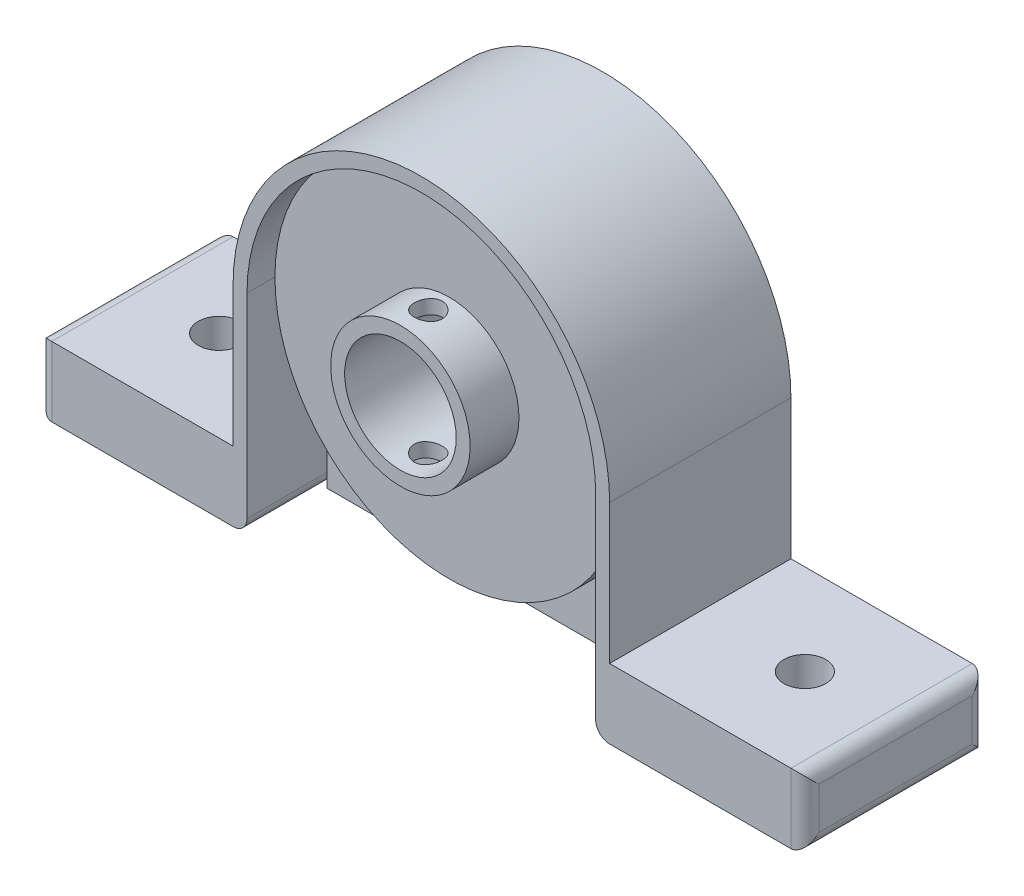
SolidWorks part; units mm, degrees
material "Cast Alloy Steel"
ref_plane "Front Plane" through (0, 0, 0) normal (0, 0, 1) x (1, 0, 0)
ref_plane "Top Plane" through (0, 0, 0) normal (0, 1, 0) x (1, 0, 0)
ref_plane "Right Plane" through (0, 0, 0) normal (1, 0, 0) x (0, 0, -1)
sketch "Sketch3" plane through (0, 0, 0) normal (0, 0, 1) x (1, 0, 0)
  line L0 (0, 0) -> (15, 0)
  line L1 (0, 0) -> (0, 5)
  line L2 (0, 5) -> (14, 5)
  line L3 (55, 0) -> (55, 5)
  line L4 (55, 5) -> (41, 5)
  line L5 (27.5, 0) -> (27.5, 15) construction
  line L6 (14, 5) -> (14, 15)
  line L7 (41, 5) -> (41, 15)
  line L8 (15, 15) -> (15, 0)
  line L9 (40, 15) -> (40, 0)
  line L10 (40, 0) -> (55, 0)
  arc A0 (15, 9.901) -> (40, 9.901) centre (27.5, 15) ccw
  circle A1 centre (27.5, 15) radius 12.5
  arc A2 (41, 15) -> (14, 15) centre (27.5, 15) ccw
  dimension "D6" = 27
  dimension "D3" = 25
  dimension "D1" = 55
  dimension "D2" = 5
  dimension "D5" = 15
extrude "Boss-Extrude1" add sketch "Sketch3" along normal blind 13
ref_plane "Plane1" through (0, 2, 0) normal (0, 1, 0) x (1, 0, 0)
sketch "Sketch6" plane through (0, 0, 13) normal (0, 0, 1) x (1, 0, 0)
  circle A0 centre (27.5, 15) radius 12.5
  circle A1 centre (27.5, 15) radius 5
  dimension "D1" = 10
extrude "Cut-Extrude2" cut sketch "Sketch6" against normal blind 2
ref_plane "Plane2" through (0, 0, 6.5) normal (0, 0, 1) x (1, 0, 0)
mirror "Mirror1" about plane through (0, 0, 6.5) normal (0, 0, 1) of "Cut-Extrude2"
sketch "Sketch7" plane through (0, 0, 13) normal (0, 0, 1) x (1, 0, 0)
  circle A0 centre (27.5, 15) radius 4.5
  dimension "D1" = 9
extrude "Cut-Extrude5" cut sketch "Sketch7" against normal blind 1.75
sketch "Sketch8" plane through (0, 0, 0) normal (0, 0, -1) x (-1, 0, 0)
  circle A0 centre (-27.5, 15) radius 4
  point P4 (-27.5, 15)
  dimension "D1" = 8
sketch "Sketch9" plane through (0, 0, 0) normal (0, 0, -1) x (-1, 0, 0)
  circle A0 centre (-27.5, 15) radius 5
extrude "Cut-Extrude6" cut sketch "Sketch9" against normal blind 1.75
sketch "Sketch10" plane through (0, 0, 11.25) normal (0, 0, 1) x (1, 0, 0)
  circle A0 centre (27.5, 15) radius 5
  dimension "D1" = 10
extrude "Boss-Extrude4" add sketch "Sketch10" along normal blind 3.25
sketch "Sketch11" plane through (0, 0, 14.5) normal (0, 0, 1) x (1, 0, 0)
  circle A0 centre (27.5, 15) radius 4
  dimension "D1" = 8
extrude "Cut-Extrude7" cut sketch "Sketch11" against normal through all
ref_plane "Plane3" through (27.5, 0, 0) normal (1, 0, 0) x (0, 0, -1)
fillet "Fillet1" radius 1 8 edges at (0, 2.5, 13) (0, 0, 6.5) (0, 2.5, 0) (0, 5, 6.5) (55, 2.5, 0) (55, 2.5, 13) (55, 0, 6.5) (55, 5, 6.5)
fillet "Fillet2" radius 1 2 edges at (40, 0, 6.5) (15, 0, 6.5)
ref_plane "Plane4" through (0, 14.25, 0) normal (0, 1, 0) x (1, 0, 0)
sketch "Sketch13" plane through (0, 14.25, 0) normal (0, 1, 0) x (1, 0, 0)
  line L1 (27.5, -14.5) -> (27.5, -12.5) construction
  line L2 (22.5, -14.5) -> (32.5, -14.5) construction
  circle A0 centre (27.5, -12.5) radius 1
  dimension "D1" = 2
  dimension "D2" = 2
extrude "Cut-Extrude11" cut sketch "Sketch13" against normal mid plane 20
sketch "Sketch15" plane through (0, 0, 0) normal (0, 1, 0) x (1, 0, 0)
  line L0 (1, -6.5) -> (54, -6.5) construction
  line L1 (1, 0) -> (1, -13) construction
  line L2 (54, -13) -> (54, 0) construction
  line L3 (54, -6.5) -> (27.5, 0) construction
  line L4 (41, 0) -> (14, 0) construction
  line L5 (27.5, 0) -> (27.5, -13) construction
  line L6 (14, -13) -> (41, -13) construction
  line L7 (6.5, -6.5) -> (6.5, -4.3967) construction
  circle A0 centre (6.5, -6.5) radius 1.5
  point P14 (27.5, -6.5)
  dimension "D2" = 3
  dimension "D1" = 21
extrude "Cut-Extrude13" cut sketch "Sketch15" along normal blind 10
ref_plane "Plane5" through (27.5, 0, 0) normal (1, 0, 0) x (0, 0, -1)
mirror "Mirror2" about plane through (27.5, 0, 0) normal (1, 0, 0) of "Cut-Extrude13"
sketch "Sketch16" plane through (0, 0, 0) normal (0, -1, 0) x (1, 0, 0)
  line L0 (6.5, 6.5) -> (48.5, 6.5) construction
  line L2 (15, 7.25) -> (40, 7.25)
  line L3 (15, 7.25) -> (15, 5.75)
  line L4 (15, 5.75) -> (40, 5.75)
  line L5 (40, 7.25) -> (40, 5.75)
  line L6 (15, 7.25) -> (40, 5.75) construction
  line L7 (15, 5.75) -> (40, 7.25) construction
  point P4 (27.5, 6.5)
  dimension "D1" = 1.5
  dimension "D2" = 25
extrude "Boss-Extrude5" add sketch "Sketch16" against normal up to surface (15 mm away)
